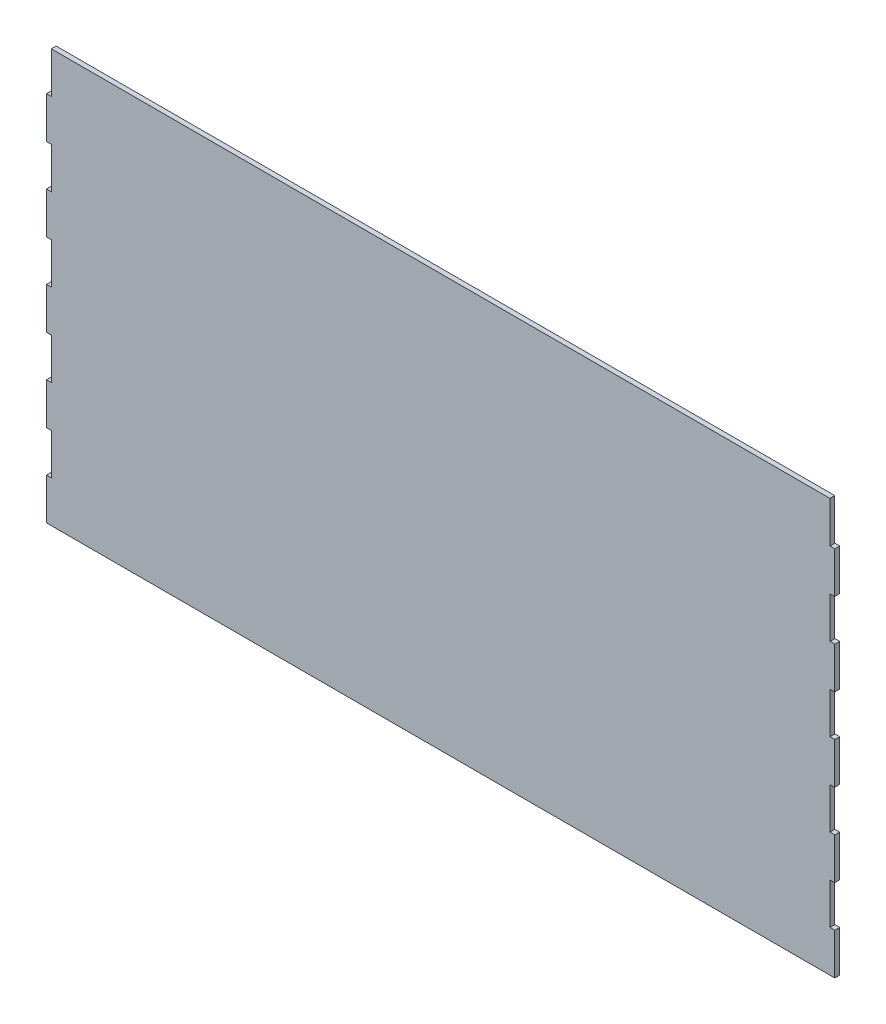
SolidWorks part; units mm, degrees
material "Pine"
ref_plane "Front Plane" through (0, 0, 0) normal (0, 0, 1) x (1, 0, 0)
ref_plane "Top Plane" through (0, 0, 0) normal (0, 1, 0) x (1, 0, 0)
ref_plane "Right Plane" through (0, 0, 0) normal (1, 0, 0) x (0, 0, -1)
sketch "Sketch1" plane through (0, 0, 0) normal (0, 0, 1) x (1, 0, 0)
  line L1 (-488.6875, 256) -> (488.6875, 256)
  line L2 (-488.6875, 256) -> (-488.6875, -256)
  line L3 (-488.6875, -256) -> (488.6875, -256)
  line L4 (488.6875, 256) -> (488.6875, -256)
  line L5 (-488.6875, 256) -> (488.6875, -256) construction
  line L6 (-488.6875, -256) -> (488.6875, 256) construction
  point P4 (0, 0)
  dimension "D1" = 977.375
  dimension "D2" = 512
  dimension "D3" = 0
  dimension "D4" = 0
extrude "Boss-Extrude1" add sketch "Sketch1" along normal blind 6
sketch "Sketch7" plane through (0, 0, 6) normal (0, 0, 1) x (1, 0, 0)
  line L0 (488.6875, -256) -> (488.6875, 256) construction
  line L1 (488.6875, -204.8) -> (482.6875, -204.8)
  line L2 (488.6875, -204.8) -> (488.6875, -153.6)
  line L3 (488.6875, -153.6) -> (482.6875, -153.6)
  line L4 (482.6875, -204.8) -> (482.6875, -153.6)
  line L5 (-488.6875, -256) -> (488.6875, -256) construction
  ellipse E0 centre (485.6875, -204.8) end of major axis (488.6875, -204.8) minor radius 0.2
  ellipse E1 centre (485.6875, -153.6) end of major axis (488.6875, -153.6) minor radius 0.2
  line M8 (488.6875, -256) -> (488.6875, 256)
  dimension "D1" = 6
  dimension "D2" = 51.2
  dimension "D3" = 51.2
  dimension "D4" = 0.2
  dimension "D5" = 0.2
extrude "Cut-Extrude3" cut sketch "Sketch7" against normal blind 10 contours E0 L3 L4 M8
pattern_linear "LPattern1" count 5 spacing 102.4 along (0, 1, 0) of "Cut-Extrude3"
sketch "Sketch8" plane through (0, 0, 6) normal (0, 0, 1) x (1, 0, 0)
  line L1 (482.6875, 256) -> (488.6875, 256)
  line L2 (482.6875, 256) -> (482.6875, 255.4193)
  line L3 (482.6875, 255.4193) -> (488.6875, 255.4193)
  line L4 (488.6875, 256) -> (488.6875, 255.4193)
  dimension "D1" = 6
  dimension "D2" = 0.5807
extrude "Cut-Extrude4" cut sketch "Sketch8" against normal blind 10
sketch "Sketch10" plane through (0, 0, 6) normal (0, 0, 1) x (1, 0, 0)
  line L0 (-488.6875, 256) -> (-488.6875, -256) construction
  line L1 (-488.6875, -204.8) -> (-482.6875, -204.8)
  line L2 (-488.6875, -204.8) -> (-488.6875, -153.6)
  line L3 (-488.6875, -153.6) -> (-482.6875, -153.6)
  line L4 (-482.6875, -204.8) -> (-482.6875, -153.6)
  line L5 (-488.6875, -256) -> (488.6875, -256) construction
  ellipse E0 centre (-485.6875, -204.8) end of major axis (-482.6875, -204.8) minor radius 0.2
  ellipse E1 centre (-485.6875, -153.6) end of major axis (-482.6875, -153.6) minor radius 0.2
  line M18 (-488.6875, 256) -> (-488.6875, -256)
  dimension "D1" = 6
  dimension "D2" = 102.4
  dimension "D3" = 51.2
  dimension "D4" = 0.2
  dimension "D5" = 0.2
extrude "Cut-Extrude5" cut sketch "Sketch10" against normal blind 10 contours E1 E0 L4 M18
pattern_linear "LPattern4" count 5 spacing 102.4 along (0, -1, 0) of "Cut-Extrude5"
sketch "Sketch11" plane through (0, 0, 6) normal (0, 0, 1) x (1, 0, 0)
  line L1 (-482.6875, 256) -> (-488.6875, 256)
  line L2 (-482.6875, 256) -> (-482.6875, 255.2668)
  line L3 (-482.6875, 255.2668) -> (-488.6875, 255.2668)
  line L4 (-488.6875, 256) -> (-488.6875, 255.2668)
  dimension "D1" = 6
  dimension "D2" = 0.7332
extrude "Cut-Extrude6" cut sketch "Sketch11" against normal blind 10 contours L3 L4 L1 L2
sketch "Sketch12" plane through (0, 0, 6) normal (0, 0, 1) x (1, 0, 0)
  line L0 (282.1875, 256) -> (282.1875, -256)
  line L1 (482.6875, 256) -> (-482.6875, 256) construction
  line L2 (-488.6875, -256) -> (488.6875, -256) construction
  line L3 (488.6875, 153.6) -> (488.6875, 204.8) construction
  line L4 (-282.1875, 256) -> (-282.1875, -256)
  line L5 (-488.6875, 204.8) -> (-488.6875, 153.6) construction
  line L6 (-206, 256) -> (-206, -256)
  dimension "D1" = 206.5
  dimension "D2" = 206.5
  dimension "D3" = 206
sketch "Sketch13" plane through (0, 0, 6) normal (0, 0, 1) x (1, 0, 0)
  line L0 (206, 256) -> (206, -256)
  line L1 (482.6875, 256) -> (-482.6875, 256) construction
  line L2 (-488.6875, -256) -> (488.6875, -256) construction
  dimension "D1" = 206
